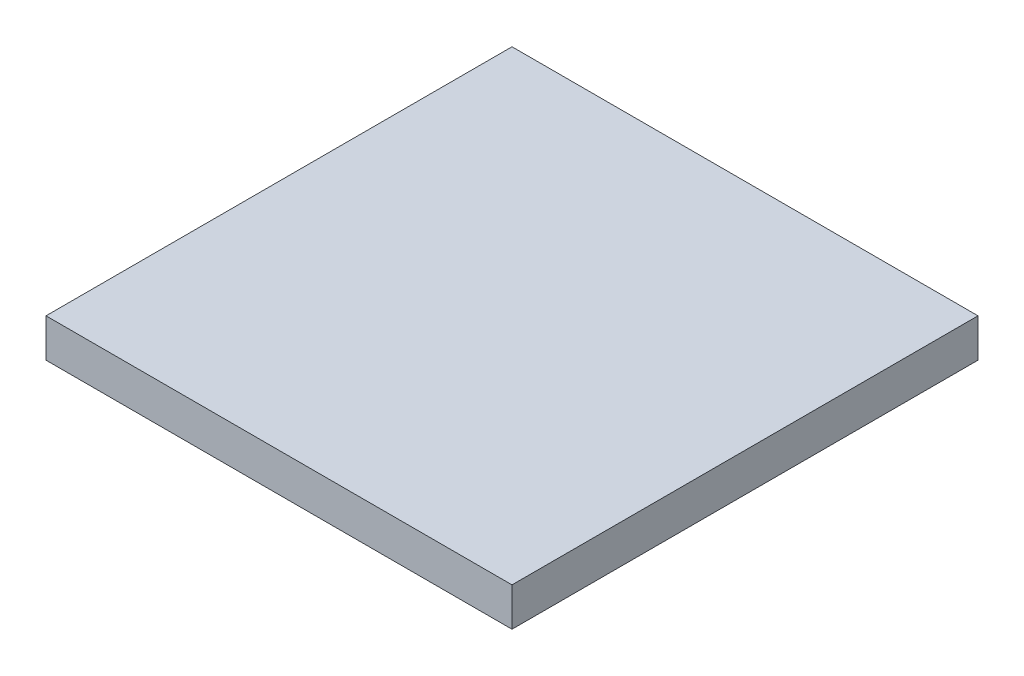
SolidWorks part; units mm, degrees
other "Markup1"
sketch "Sketch2" plane through (20, 3.3, 20) normal (0.5446, 0.2409, 0.8033) x (0.836, -0.0797, -0.5429)
ref_plane "Front Plane" through (0, 0, 0) normal (0, 0, 1) x (1, 0, 0)
ref_plane "Top Plane" through (0, 0, 0) normal (0, 1, 0) x (1, 0, 0)
ref_plane "Right Plane" through (0, 0, 0) normal (1, 0, 0) x (0, 0, -1)
sketch "Sketch1" plane through (0, 0, 0) normal (0, 1, 0) x (1, 0, 0)
  line L1 (-20, -20) -> (20, -20)
  line L2 (-20, -20) -> (-20, 20)
  line L3 (-20, 20) -> (20, 20)
  line L4 (20, -20) -> (20, 20)
  line L5 (-20, -20) -> (20, 20) construction
  line L6 (-20, 20) -> (20, -20) construction
  point P0 (0, 0)
  dimension "D1" = 40
  dimension "D2" = 40
extrude "Boss-Extrude1" add sketch "Sketch1" along normal blind 3.3
